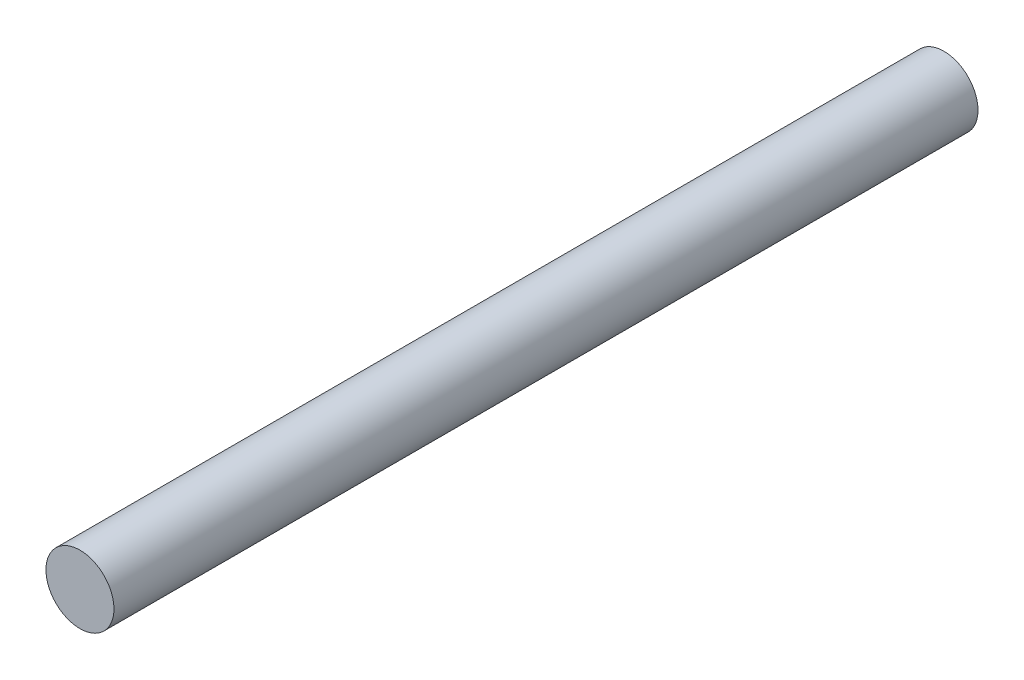
SolidWorks part; units mm, degrees
ref_plane "Front Plane" through (0, 0, 0) normal (0, 0, 1) x (1, 0, 0)
ref_plane "Top Plane" through (0, 0, 0) normal (0, 1, 0) x (1, 0, 0)
ref_plane "Right Plane" through (0, 0, 0) normal (1, 0, 0) x (0, 0, -1)
sketch "Sketch1" plane through (0, 0, 0) normal (0, 0, 1) x (1, 0, 0)
  circle A0 centre (0, 0) radius 3
  dimension "D1" = 6
extrude "Boss-Extrude1" add sketch "Sketch1" along normal blind 76.2
